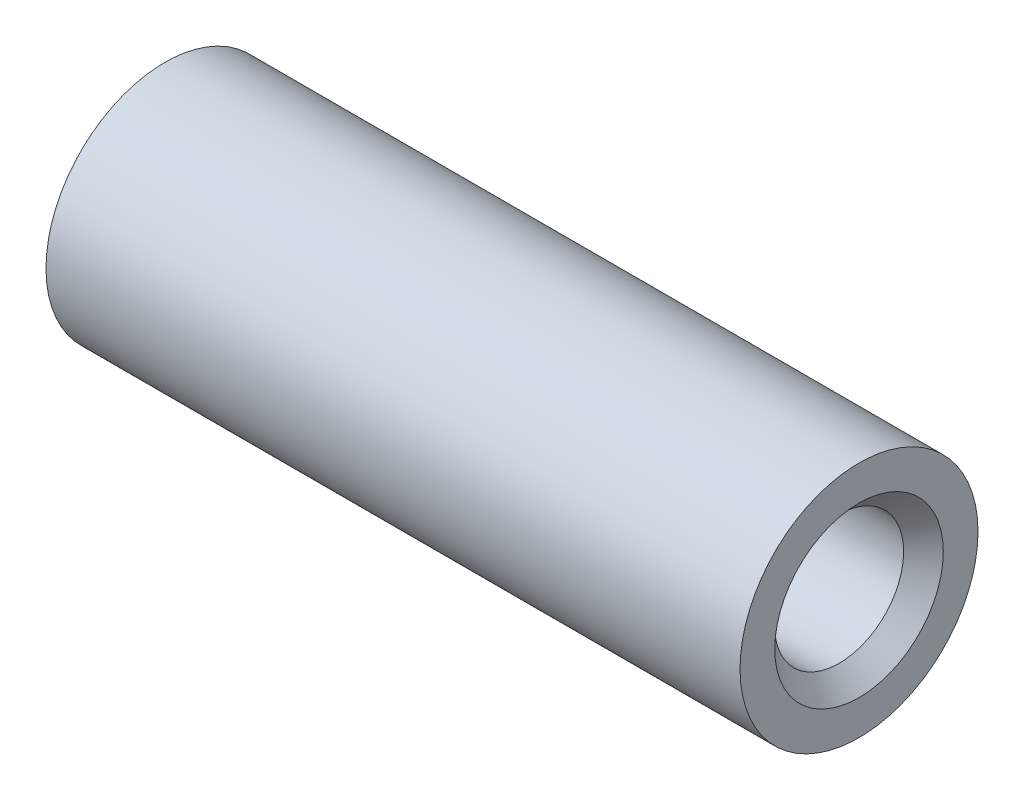
SolidWorks part; units mm, degrees
ref_plane "Спереди" through (0, 0, 0) normal (0, 0, 1) x (1, 0, 0)
ref_plane "Сверху" through (0, 0, 0) normal (0, 1, 0) x (1, 0, 0)
ref_plane "Справа" through (0, 0, 0) normal (1, 0, 0) x (0, 0, -1)
sketch "Эскиз1" plane through (0, 0, 0) normal (1, 0, 0) x (0, 0, -1)
  circle A0 centre (0, 0) radius 3.25
  circle A1 centre (0, 0) radius 6
  dimension "D1" = 6.5
  dimension "D2" = 12
extrude "Бобышка-Вытянуть1" add sketch "Эскиз1" along normal blind 35
chamfer "Фаска1" distance 1 angle 45 2 edges at (0, 0, -3.25) (35, 0, -3.25)
